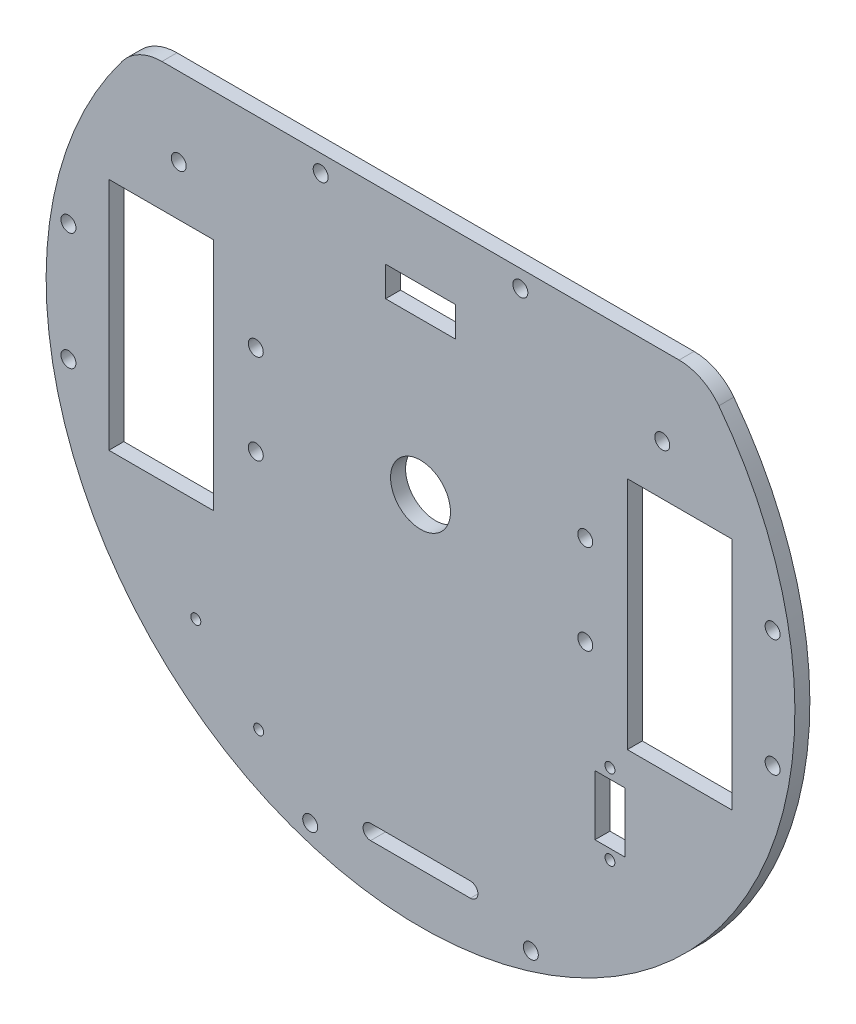
SolidWorks part; units mm, degrees
ref_plane "Front Plane" through (0, 0, 0) normal (0, 0, 1) x (1, 0, 0)
ref_plane "Top Plane" through (0, 0, 0) normal (0, 1, 0) x (1, 0, 0)
ref_plane "Right Plane" through (0, 0, 0) normal (1, 0, 0) x (0, 0, -1)
sketch "Sketch1" plane through (0, 0, 0) normal (0, 0, 1) x (1, 0, 0)
  line L0 (0, 0) -> (-33.5, 0) construction
  line L2 (75, 0) -> (71.5, 0) construction
  line L6 (-62.4303, 23.5) -> (-41.4303, 23.5)
  line L13 (-62.4303, 23.5) -> (-62.4303, -23.5)
  line L14 (-62.4303, -23.5) -> (-41.4303, -23.5)
  line L15 (-41.4303, 23.5) -> (-41.4303, -23.5)
  line L16 (-62.4303, 23.5) -> (-41.4303, -23.5) construction
  line L17 (-62.4303, -23.5) -> (-41.4303, 23.5) construction
  line L26 (53.2657, 42.2701) -> (-53.2657, 42.2701) construction
  line L39 (0, 0) -> (0, 100.1926) construction
  line L41 (-10, -63.5) -> (10, -63.5) construction
  line L42 (-10, -62) -> (10, -62)
  line L43 (-10, -65) -> (10, -65)
  line L45 (-51.9303, 23.5) -> (-51.9303, 50.6806) construction
  line L46 (-51.7963, 49.2701) -> (51.7963, 49.2701)
  line L59 (162.9489, -263.5978) -> (-50.3441, -45.7798) construction
  line L60 (-53.5344, -35.3754) -> (-29.163, -60.2638) construction
  line L61 (40.944, -23.1127) -> (40.944, -49.5933) construction
  line L63 (34.944, -30.3857) -> (40.944, -30.3857)
  line L64 (34.944, -30.3857) -> (34.944, -42.3857)
  line L65 (34.944, -42.3857) -> (40.944, -42.3857)
  line L66 (40.944, -30.3857) -> (40.944, -42.3857)
  line L67 (34.944, -30.3857) -> (40.944, -42.3857) construction
  line L68 (34.944, -42.3857) -> (40.944, -30.3857) construction
  line L78 (62.4303, -23.5) -> (41.4303, -23.5)
  line L79 (41.4303, 23.5) -> (41.4303, -23.5)
  line L80 (62.4303, 23.5) -> (41.4303, 23.5)
  line L81 (62.4303, 23.5) -> (62.4303, -23.5)
  line L83 (-33, 9) -> (-33, -9) construction
  line L84 (-7, 36.5) -> (7, 36.5)
  line L88 (-71.5, 0) -> (-79.7576, 0) construction
  line L89 (-7, 36.5) -> (-7, 30.5)
  line L90 (-7, 30.5) -> (7, 30.5)
  line L91 (7, 36.5) -> (7, 30.5)
  line L92 (-7, 36.5) -> (7, 30.5) construction
  line L93 (-7, 30.5) -> (7, 36.5) construction
  circle A4 centre (22.0947, -68.0592) radius 1.5
  circle A5 centre (-22.0947, -68.0005) radius 1.5
  arc A13 (-53.2657, 42.2701) -> (53.2657, 42.2701) centre (0, 0) ccw construction
  circle A14 centre (0, 0) radius 6
  circle A16 centre (-33, 9) radius 1.5
  circle A17 centre (-33, -9) radius 1.5
  circle A18 centre (48.4303, 33.5) radius 1.5
  arc A25 (-10, -62) -> (-10, -65) centre (-10, -63.5) ccw
  arc A26 (10, -65) -> (10, -62) centre (10, -63.5) ccw
  circle A27 centre (20, 45.7701) radius 1.5
  circle A28 centre (-20, 45.7701) radius 1.5
  circle A29 centre (-48.4303, 33.5) radius 1.5
  arc A32 (-59.765, 45.3117) -> (59.765, 45.3117) centre (0, 0) ccw
  circle A33 centre (-32.4192, -56.9385) radius 1
  circle A34 centre (-45.0128, -44.0777) radius 1
  circle A35 centre (37.944, -28.3857) radius 1
  circle A36 centre (37.944, -44.3857) radius 1
  circle A37 centre (0, 0) radius 71.5 construction
  circle A38 centre (-70.5279, 11.75) radius 1.5
  circle A39 centre (-70.5279, -11.75) radius 1.5
  circle A40 centre (70.5279, -11.75) radius 1.5
  circle A41 centre (70.5279, 11.75) radius 1.5
  arc A42 (59.765, 45.3117) -> (51.7963, 49.2701) centre (51.7963, 39.2701) ccw
  arc A43 (-51.7963, 49.2701) -> (-59.765, 45.3117) centre (-51.7963, 39.2701) ccw
  circle A44 centre (33, -9) radius 1.5
  circle A45 centre (33, 9) radius 1.5
  point P9 (0, 33.5)
  point P24 (0, 0)
  point P26 (0, 0)
  point P34 (-51.9303, 0)
  point P63 (0, 0)
  point P65 (0, -63.5)
  point P76 (37.944, -36.3857)
  dimension "D5" = 150
  dimension "D6" = 12
  dimension "D7" = 7
  dimension "D13" = 3
  dimension "D14" = 7
  dimension "D16" = 2
  dimension "D19" = 1.5
  dimension "D21" = 3
  dimension "D23" = 3
  dimension "D26" = 3.5
  dimension "D8" = 7
  dimension "D15" = 2
  dimension "D17" = 5
  dimension "D27" = 3
  dimension "D28" = 2
  dimension "D29" = 2
  dimension "D34" = 2
  dimension "D37" = 10
  dimension "D38" = 41.4303
  dimension "D39" = 11.75
  dimension "D40" = 3
  dimension "D42" = 3.5
  dimension "D2" = 3.5
  dimension "D9" = 6
  dimension "D10" = 14
  dimension "D11" = 21
  dimension "D12" = 47
  dimension "D18" = 20
  dimension "D20" = 65
  dimension "D22" = 18
  dimension "D24" = 10
  dimension "D25" = 3.5
  dimension "D4" = 3.5
  dimension "D30" = 16
  dimension "D31" = 12
  dimension "D32" = 6
  dimension "D33" = 3
  dimension "D35" = 20
  dimension "D36" = 20
  dimension "D41" = 33
extrude "Boss-Extrude2" add sketch "Sketch1" along normal blind 3
